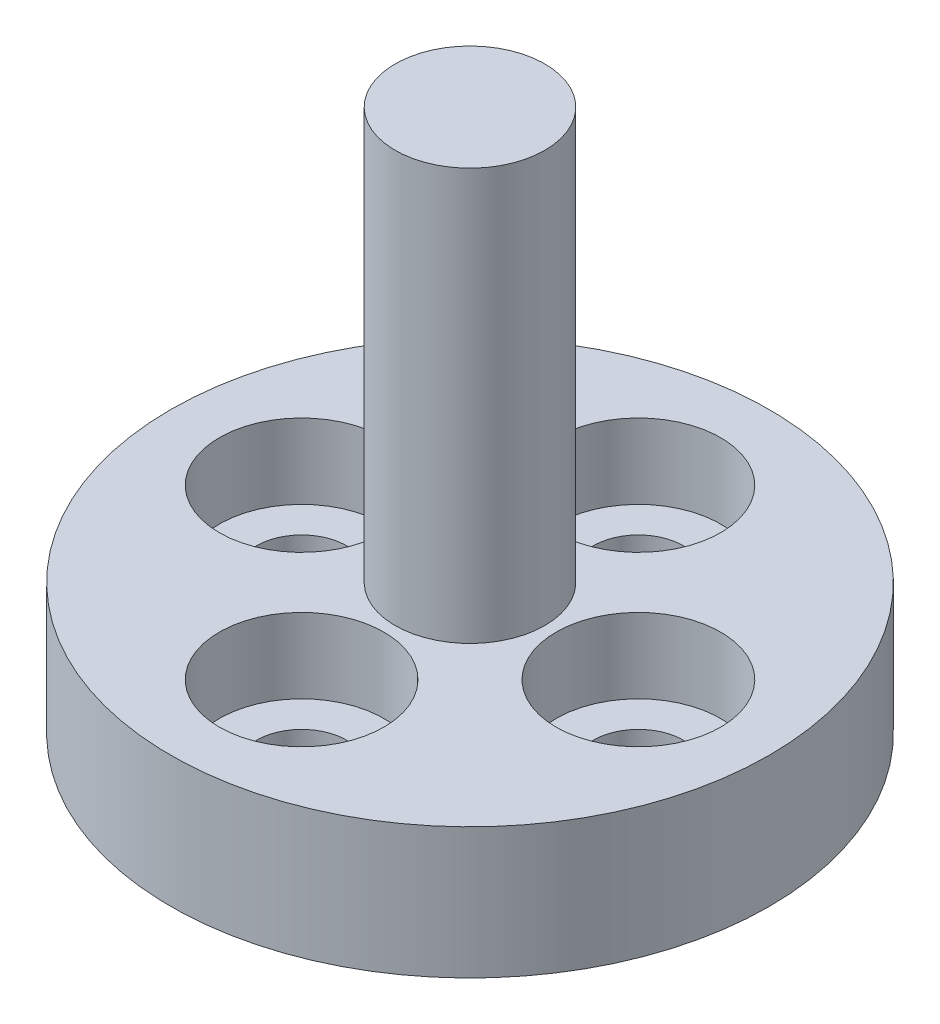
SolidWorks part; units mm, degrees
ref_plane "Front Plane" through (0, 0, 0) normal (0, 0, 1) x (1, 0, 0)
ref_plane "Top Plane" through (0, 0, 0) normal (0, 1, 0) x (1, 0, 0)
ref_plane "Right Plane" through (0, 0, 0) normal (1, 0, 0) x (0, 0, -1)
sketch "Sketch3" plane through (0, 0, 0) normal (0, 0, 1) x (1, 0, 0)
  line L0 (0, 0) -> (0, 14.5)
  line L1 (0, 14.5) -> (2, 14.5)
  line L2 (2, 14.5) -> (2, 3.5)
  line L3 (2, 3.5) -> (8, 3.5)
  line L4 (8, 3.5) -> (8, 0)
  line L5 (8, 0) -> (0, 0)
  dimension "D1" = 2
  dimension "D2" = 8
  dimension "D3" = 11
  dimension "D4" = 14.5
revolve "Revolve1" add sketch "Sketch3" angle 360 about L0
sketch "Sketch4" plane through (0, 3.5, 0) normal (0, 1, 0) x (1, 0, 0)
  circle A0 centre (0, 0) radius 4.5
  dimension "D1" = 9
sketch "Sketch7" plane through (0, 3.5, 0) normal (0, 1, 0) x (1, 0, 0)
  circle A0 centre (0, 0) radius 4.5 construction
  point P0 (-4.5, 0)
  point P4 (0, 4.5)
  point P6 (4.5, 0)
  point P8 (0, -4.5)
hole_wizard "CBORE for M2 SHCS1" positions "Sketch7" profile "Sketch6" counterbore size "M2" standard "ANSI Metric" end condition through all
sketch "Sketch6" plane through (-4.5, 3.5, 0) normal (1, 0, 0) x (0, 0, 1)
  line L0 (0, 0) -> (0, 3.5)
  line L1 (0, 3.5) -> (1.2, 3.5)
  line L3 (1.2, 3.5) -> (1.2, 2)
  line L4 (1.2, 2) -> (2.2, 2)
  line L5 (2.2, 2) -> (2.2, 0)
  line L7 (2.2, 0) -> (0, 0)
  line L11 (0, -6.35) -> (0, 107.95) construction
  dimension "Thru Hole Dia." = 2.4
  dimension "Thru Hole Depth" = 3.5
  dimension "C'Bore Dia." = 4.4
  dimension "C'Bore Depth" = 2
